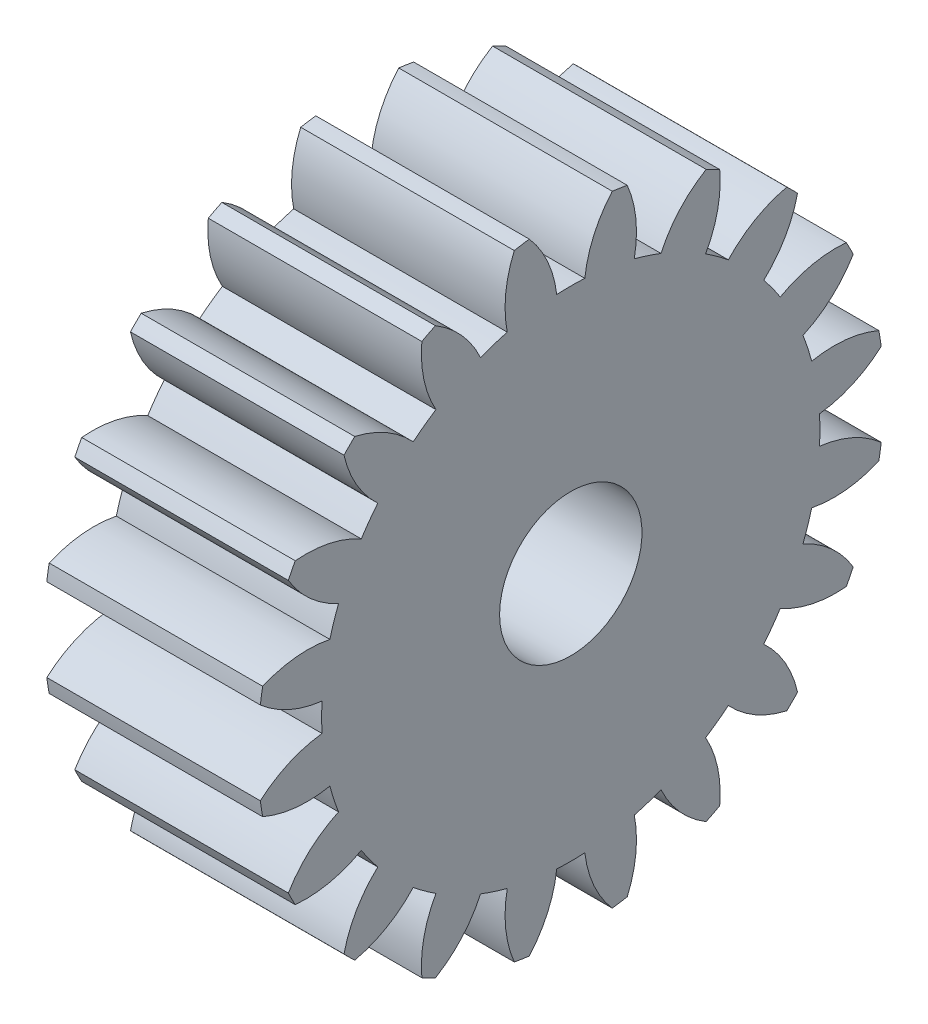
SolidWorks part; units mm, degrees
material "Alloy Steel"
ref_plane "Plane1" through (0, 0, 0) normal (0, 0, 1) x (1, 0, 0)
ref_plane "Plane2" through (0, 0, 0) normal (0, 1, 0) x (1, 0, 0)
ref_plane "Plane3" through (0, 0, 0) normal (1, 0, 0) x (0, 0, -1)
other "Configuration Table"
sketch "HoldingSke" plane through (0, 0, 0) normal (0, 1, 0) x (1, 0, 0)
  line L0 (0, 0) -> (0.4698, -0.171)
  line L1 (-15, 0) -> (100, 0) construction
  line L2 (0, 0) -> (-2.1039, 2.3779)
  line L3 (0, 0) -> (-11.863, 4.5341)
  line L4 (0, 0) -> (8.1152, 2.9537)
  line L5 (0, 0) -> (-46.8476, -17.4728)
  line L6 (0, 0) -> (-12.4344, -8.3896)
  line L7 (-2.1039, 2.3779) -> (8.6586, 51.2059)
  line L8 (-76.2, 54.61) -> (-74.4, 54.61)
  line L9 (-71.009, 38.7566) -> (-53.1078, 45.2721)
  line L10 (-76.2, 71.12) -> (104.1128, 71.12)
  line L11 (0, 0) -> (-15, 0)
  line L12 (-76.2, 101.6) -> (-76.133, 101.6)
  line L13 (24.9733, 27.94) -> (52.9518, 28.4284)
  line L14 (24.9733, 27.94) -> (24.9743, 27.94)
  line L15 (24.9733, 27.94) -> (100.4006, 29.5858)
  line L16 (-63.627, -2) -> (-12.827, -2)
  circle A0 centre (0, 0) radius 5
  circle A1 centre (0, 0) radius 17.499
  circle A2 centre (0, 0) radius 37.5
  circle A3 centre (0, 0) radius 5
  dimension "MHD" = 34.998
  dimension "Hub_dia" = 75
  dimension "Bore" = 10
  dimension "MBD" = 10
  dimension "Num_teeth" = 20
  dimension "Pitch" = 0.5
  dimension "Overall_len" = 50
  dimension "Show_teeth" = 20
  dimension "Thickness" = 15
  dimension "OAL" = 50.0001
  dimension "T_dim" = 1.8
  dimension "Ap" = 20
  dimension "H" = 19.05
  dimension "Pitch_radius" = 180.3128
  dimension "Width" = 15
  dimension "Backlash" = 0.067
  dimension "Addendum_fac" = 1
  dimension "Dedendum_fac" = 1.25
  dimension "Clearance_fac" = 0.25
  dimension "Dedendum_add" = 0.001
  dimension "Module" = 2
sketch "BasProSke" plane through (0, 0, 0) normal (0, 1, 0) x (1, 0, 0)
  line L0 (-10, 0) -> (60, 0) construction
  line L1 (0, 0) -> (0, 22)
  line L2 (0, 0) -> (15, 0)
  line L3 (15, 0) -> (15, 22)
  line L4 (15, 22) -> (0, 22)
  dimension "Thickness" = 15
  dimension "Diameter" = 44
revolve "Base-Revolve" add sketch "BasProSke" angle 360 about L0
sketch "TooCutSke" plane through (0, 0, 0) normal (1, 0, 0) x (0, 0, -1)
  line L1 (0, 0) -> (0, 107) construction
  line L2 (0, 0) -> (-1.6864, 19.9288) construction
  line L3 (0, 0) -> (-6.2409, 39.4033) construction
  line L4 (-1.6864, 19.9288) -> (-3.1204, 19.7016) construction
  arc A0 (0.9862, 17.4712) -> (-0.9862, 17.4712) centre (0, 0) ccw
  arc A1 (2.9329, 21.8293) -> (-2.9329, 21.8293) centre (0, 0) ccw
  circle A2 centre (0, 0) radius 20 construction
  circle A3 centre (0, 0) radius 18.7939 construction
  arc A4 (-0.9862, 17.4712) -> (-2.9329, 21.8293) centre (-8.9313, 16.536) ccw
  arc A5 (2.9329, 21.8293) -> (0.9862, 17.4712) centre (8.9313, 16.536) ccw
  dimension "Root_dia" = 34.998
  dimension "Overcut_dia" = 44.0508
  dimension "Pitch_dia" = 40
  dimension "Base_dia" = 37.5877
  dimension "Flank_rad" = 8
  dimension "Half_ang" = 9
  dimension "Half_CT" = 1.4519
extrude "ToothCut" cut sketch "TooCutSke" along normal through all
fillet "Breaks" [suppressed] radius 0.04
fillet "RootFillets" [suppressed] radius 0.501
pattern_circular "TeethCuts" count 20 every 18 about axis through (-10, 0, 0) along (1, 0, 0) of "ToothCut", "RootFillets", "Breaks"
sketch "HubNeaOneSke" plane through (0, 0, 0) normal (-1, 0, 0) x (0, 0, 1)
  circle A0 centre (0, 0) radius 17.499
  dimension "Diameter" = 34.998
extrude "HubNearOne" [suppressed] add sketch "HubNeaOneSke" along normal blind 35.0001
sketch "HubNeaBotSke" plane through (0, 0, 0) normal (-1, 0, 0) x (0, 0, 1)
  circle A0 centre (0, 0) radius 17.499
  dimension "Diameter" = 34.998
extrude "HubNearBoth" [suppressed] add sketch "HubNeaBotSke" along normal blind 17.5
ref_plane "FarPln" through (15, 0, 0) normal (1, 0, 0) x (0, 0, -1)
sketch "HubFarSke" plane through (15, 0, 0) normal (1, 0, 0) x (0, 0, -1)
  circle A0 centre (0, 0) radius 17.499
  dimension "Diameter" = 34.998
extrude "HubFar" [suppressed] add sketch "HubFarSke" along normal blind 17.5
sketch "BorSke" plane through (0, 0, 0) normal (1, 0, 0) x (0, 0, -1)
  circle A0 centre (0, 0) radius 5
  dimension "Diameter" = 10
extrude "Bore" cut sketch "BorSke" along normal mid plane 100.0001
sketch "KeySke" plane through (0, 0, 0) normal (1, 0, 0) x (0, 0, -1)
  line L0 (-2, 0) -> (-2, 6.8)
  line L1 (-2, 6.8) -> (2, 6.8)
  line L2 (2, 6.8) -> (2, 0)
  line L3 (0, 0) -> (0, 34) construction
  line L4 (-2, 0) -> (2, 0)
  dimension "Offset" = 6.8
  dimension "Width" = 4
extrude "Keyway" [suppressed] cut sketch "KeySke" along normal mid plane 100.0001
pattern_circular "Keyway2" [suppressed] count 2 every 90 about axis through (-10, 0, 0) along (1, 0, 0)
equation "' \"Module@HoldingSke\" = 6.35"
equation "' \"Num_teeth@HoldingSke\" = 12"
equation "' \"Ap@HoldingSke\" =  20"
equation "' \"Ap@HoldingSke\" = 20"
equation "' \"Width@HoldingSke\" = 0.5 * 25.4"
equation "' \"Hub_dia@HoldingSke\"= 1 * 25.4"
equation "' \"Hub_dia@HoldingSke\" = 1 * 25.4"
equation "' \"Overall_len@HoldingSke\" = 1.0 * 25.4"
equation "' \"Bore@HoldingSke\" = 0.75 * 25.4"
equation "' \"T_dim@HoldingSke\" = 0.1 * 25.4"
equation "' \"Width@KeySke\" = 0.25 * 25.4"
equation "' \"Show_teeth@HoldingSke\" = 13"
equation "' \"Backlash@HoldingSke\" = 0.009 * 25.4"
equation "' \"Addendum_fac@HoldingSke\" = 1.0"
equation "' \"Dedendum_fac@HoldingSke\" = 1.25"
equation "' \"Dedendum_add@HoldingSke\" = 0.00005 * 25.4"
equation "' \"Clearance_fac@HoldingSke\" = 0.25"
equation "\"Pitch@HoldingSke\" = 1 / \"Module@HoldingSke\""
equation "\"Overcut_dia@TooCutSke\" = (\"Num_teeth@HoldingSke\" + 2 * \"Addendum_fac@HoldingSke\") / \"Pitch@HoldingSke\" + 0.002 * 25.4"
equation "\"Pitch_dia@TooCutSke\" = \"Num_teeth@HoldingSke\" / \"Pitch@HoldingSke\""
equation "\"Base_dia@TooCutSke\" = \"Num_teeth@HoldingSke\" / \"Pitch@HoldingSke\" * cos((\"Ap@HoldingSke\"  * 3.14159265 / 180))"
equation "\"Root_dia@TooCutSke\" = (\"Num_teeth@HoldingSke\" + 2) / \"Pitch@HoldingSke\" - 2 * (\"Addendum_fac@HoldingSke\" + \"Dedendum_fac@HoldingSke\") / \"Pitch@HoldingSke\" - \"Dedendum_add@HoldingSke\" * 2"
equation "\"Half_ang@TooCutSke\" = 180 / \"Num_teeth@HoldingSke\""
equation "\"Half_CT@TooCutSke\" = \"Num_teeth@HoldingSke\" / \"Pitch@HoldingSke\" * sin((3.14159265 / 2 / \"Num_teeth@HoldingSke\")) / 2 - 7 * \"Backlash@HoldingSke\" / 4"
equation "\"Flank_rad@TooCutSke\" = \"Num_teeth@HoldingSke\" / \"Pitch@HoldingSke\" / 5"
equation "\"Radius@RootFillets\" = \"Clearance_fac@HoldingSke\" / \"Pitch@HoldingSke\" + \"Dedendum_add@HoldingSke\""
equation "\"Break_rad@Breaks\" = 0.02 / \"Pitch@HoldingSke\""
equation "\"Thickness@HoldingSke\" = \"Width@HoldingSke\""
equation "\"OAL@HoldingSke\" = \"Thickness@HoldingSke\""
equation "\"MHD@HoldingSke\" = (\"Num_teeth@HoldingSke\" + 2) / \"Pitch@HoldingSke\" - 2 * (\"Addendum_fac@HoldingSke\" + \"Dedendum_fac@HoldingSke\")  / \"Pitch@HoldingSke\" - \"Dedendum_add@HoldingSke\" * 2"
equation "\"MBD@HoldingSke\" = (\"Num_teeth@HoldingSke\" + 2) / \"Pitch@HoldingSke\" - 2 * (\"Addendum_fac@HoldingSke\" + \"Dedendum_fac@HoldingSke\")  / \"Pitch@HoldingSke\" - \"Dedendum_add@HoldingSke\" * 2 - 0.002 * 25.4"
equation "\"MHD@HoldingSke\" = ((sgn( \"MHD@HoldingSke\" - \"Hub_dia@HoldingSke\" )-1)*( \"MHD@HoldingSke\" - \"Hub_dia@HoldingSke\" ))/-2+ \"Hub_dia@HoldingSke\""
equation "\"MBD@HoldingSke\" = ((sgn( \"MBD@HoldingSke\" - \"Bore@HoldingSke\" )-1)*( \"MBD@HoldingSke\" - \"Bore@HoldingSke\" ))/-2+ \"Bore@HoldingSke\""
equation "\"OAL@HoldingSke\" = ((sgn( \"OAL@HoldingSke\" - \"Overall_len@HoldingSke\" )+1)*( \"OAL@HoldingSke\" - \"Overall_len@HoldingSke\" ))/2 + \"Overall_len@HoldingSke\" + 0.000002 * 25.4"
equation "\"Num_teeth@TeethCuts\" = int( \"Show_teeth@HoldingSke\" ) + 1"
equation "\"Num_teeth@TeethCuts\" = ((sgn( \"Num_teeth@TeethCuts\" - \"Num_teeth@HoldingSke\" )-1)*( \"Num_teeth@TeethCuts\" - \"Num_teeth@HoldingSke\" ))/-2+ \"Num_teeth@HoldingSke\""
equation "\"Num_teeth@TeethCuts\" = ((sgn( \"Num_teeth@TeethCuts\" - 2.0)+1)*( \"Num_teeth@TeethCuts\" - 2.0))/2 +2.0"
equation "\"Angle@TeethCuts\" = 360.0 / \"Num_teeth@HoldingSke\""
equation "\"Diameter@BasProSke\" = (\"Num_teeth@HoldingSke\" + 2 * \"Addendum_fac@HoldingSke\") / \"Pitch@HoldingSke\""
equation "\"Thickness@BasProSke\"  = \"Thickness@HoldingSke\""
equation "' \"Fillet_rad@BasProSke\" =  \"Thickness@HoldingSke\" * 0.05"
equation "' \"Fillet_rad@BasProSke\" = \"Thickness@HoldingSke\" * 0.05"
equation "\"MHD@HoldingSke\" = ((sgn( \"MHD@HoldingSke\" - \"Root_dia@TooCutSke\" )-1)*( \"MHD@HoldingSke\" - \"Root_dia@TooCutSke\" ))/-2+ \"Root_dia@TooCutSke\""
equation "\"Diameter@HubNeaOneSke\" = \"MHD@HoldingSke\""
equation "\"Length@HubNearOne\" = \"OAL@HoldingSke\" - \"Thickness@BasProSke\""
equation "\"Diameter@HubNeaBotSke\" = \"MHD@HoldingSke\""
equation "\"Length@HubNearBoth\" = ( \"OAL@HoldingSke\" - \"Thickness@BasProSke\" ) / 2.0"
equation "\"Thickness@FarPln\" = \"Thickness@BasProSke\""
equation "\"Diameter@HubFarSke\" = \"MHD@HoldingSke\""
equation "\"Length@HubFar\" = ( \"OAL@HoldingSke\" - \"Thickness@BasProSke\" ) / 2.0"
equation "\"Diameter@BorSke\" = \"MBD@HoldingSke\""
equation "\"D1@Bore\" = \"OAL@HoldingSke\" * 2.0"
equation "\"D1@Keyway\" = \"OAL@HoldingSke\" * 2.0"
equation "\"Offset@KeySke\" = \"T_dim@HoldingSke\" + \"MBD@HoldingSke\" / 2.0"
